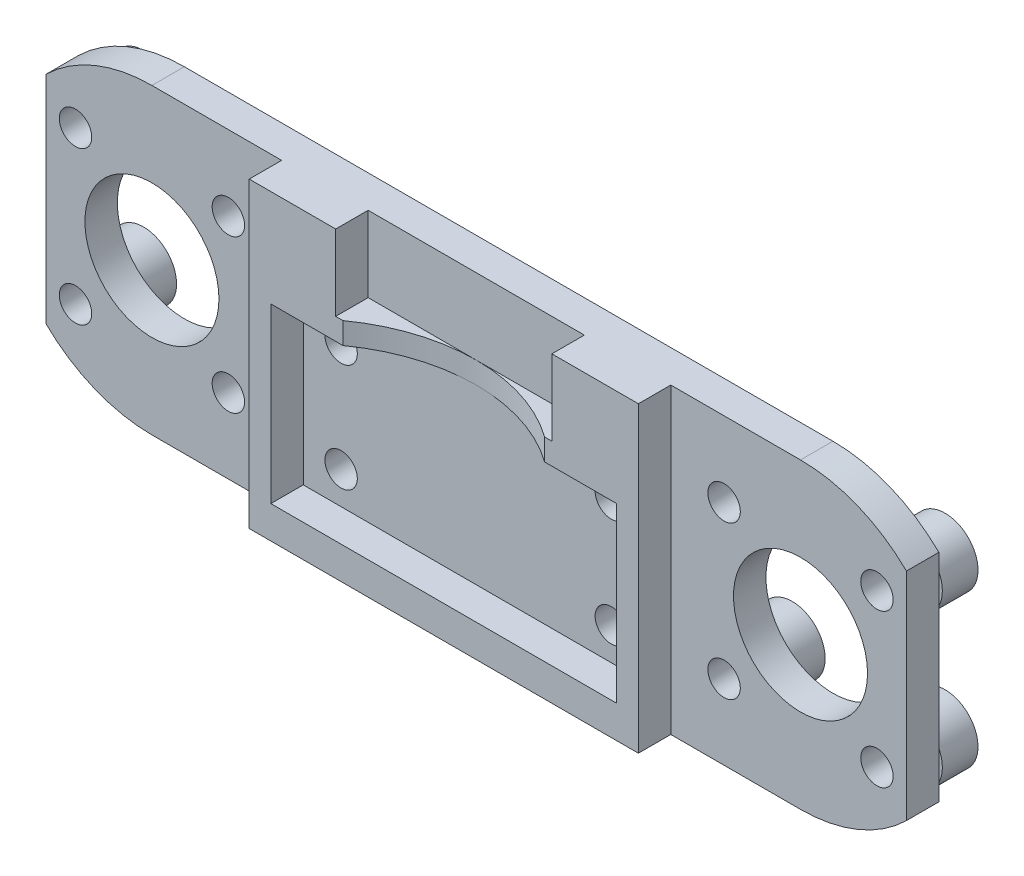
SolidWorks part; units mm, degrees
ref_plane "Front Plane" through (0, 0, 0) normal (0, 0, 1) x (1, 0, 0)
ref_plane "Top Plane" through (0, 0, 0) normal (0, 1, 0) x (1, 0, 0)
ref_plane "Right Plane" through (0, 0, 0) normal (1, 0, 0) x (0, 0, -1)
sketch "Sketch1" plane through (0, 0, 0) normal (0, 0, 1) x (1, 0, 0)
  line L0 (-39.8, 9.998) -> (-39.8, -9.998)
  line L1 (-30, -14) -> (30, -14)
  line L2 (-30, 14) -> (30, 14)
  line L6 (-30, 0) -> (30, 0) construction
  line L7 (39.8, 9.998) -> (39.8, -9.998)
  arc A0 (-30, 14) -> (-39.8, 9.998) centre (-30, 0) ccw
  arc A1 (-39.8, -9.998) -> (-30, -14) centre (-30, 0) ccw
  circle A2 centre (-30, 0) radius 6.2
  arc A7 (30, -14) -> (39.8, -9.998) centre (30, 0) ccw
  arc A8 (39.8, 9.998) -> (30, 14) centre (30, 0) ccw
  circle A9 centre (30, 0) radius 6.2
  point P7 (0, 0)
  point P8 (0, 0)
  point P18 (-30, 0)
  point P25 (30, 0)
  point P36 (30, 0)
  dimension "D2" = 9.8
  dimension "D3" = 12.4
  dimension "D4" = 14
  dimension "D1" = 28
  dimension "D7" = 60
extrude "Main" add sketch "Sketch1" along normal mid plane 3
sketch "Sketch2" plane through (0, 0, 1.5) normal (0, 0, -1) x (-1, 0, 0)
  line L0 (30, -14) -> (-30, -14) construction
  line L1 (39.8, 9.998) -> (39.8, -9.998) construction
  line L2 (18, 14) -> (10, 14)
  line L3 (18, 14) -> (18, -14)
  line L4 (18, -14) -> (-18, -14)
  line L5 (-18, 14) -> (-18, -14)
  line L6 (16, 5) -> (-16, 5)
  line L7 (16, 5) -> (16, -11)
  line L8 (16, -11) -> (-16, -11)
  line L9 (-16, 5) -> (-16, -11)
  line L10 (-39.8, -9.998) -> (-39.8, 9.998) construction
  line L11 (-30, 14) -> (30, 14) construction
  line L13 (-30, 14) -> (30, 14) construction
  line L14 (10, 14) -> (10, 7)
  line L15 (10, 7) -> (-10, 7)
  line L16 (-10, 7) -> (-10, 14)
  line L17 (-10, 14) -> (-18, 14)
  point P13 (0, -14)
  point P14 (0, 7)
  point P22 (0, 5)
  point P27 (16, -3)
  point P29 (0, -11)
  dimension "D1" = 16
  dimension "D2" = 36
  dimension "D4" = 7
  dimension "D5" = 32
  dimension "D6" = 79.6
  dimension "D9" = 3
  dimension "D10" = 2
  dimension "D11" = 20
  dimension "D12" = 3
extrude "Framework" add sketch "Sketch2" against normal blind 3
sketch "Sketch3" plane through (0, 0, -1.5) normal (0, 0, -1) x (-1, 0, 0)
  line L6 (16, 5) -> (16, -11) construction
  line L9 (16, -11) -> (-16, -11) construction
  circle A1 centre (12.5, -8) radius 1.5
  point P0 (16, -3)
  dimension "D1" = 3
  dimension "D2" = 5
  dimension "D3" = 12.5
  dimension "D4" = 8
  dimension "D5" = 3.5
  dimension "D6" = 3
extrude "FixHole" cut sketch "Sketch3" against normal through all
pattern_linear "HolePattern" count 2 spacing 25 along (1, 0, 0) count 2 spacing 10 along (0, 1, 0) of "FixHole"
sketch "Sketch4" plane through (0, 0, -1.5) normal (0, 0, 1) x (1, 0, 0)
  line L0 (-37.0711, 7.0711) -> (-22.9289, -7.0711) construction
  line L1 (-37.0711, -7.0711) -> (-22.9289, 7.0711) construction
  circle A0 centre (-37.0711, 7.0711) radius 3.05
  circle A1 centre (-22.9289, -7.0711) radius 3.05
  circle A2 centre (-22.9289, 7.0711) radius 3.05
  circle A3 centre (-37.0711, -7.0711) radius 3.05
  circle A4 centre (-37.0711, 7.0711) radius 1.5
  circle A5 centre (-22.9289, 7.0711) radius 1.5
  circle A6 centre (-30, 0) radius 6.2 construction
  circle A7 centre (-30, 0) radius 6.2 construction
  circle A8 centre (-37.0711, -7.0711) radius 1.5
  circle A9 centre (-22.9289, -7.0711) radius 1.5
  point P6 (-30, 0)
  point P10 (-30, 0)
  dimension "D1" = 6.1
  dimension "D3" = 3
  dimension "D2" = 20
extrude "ForLMK6UU" add sketch "Sketch4" against normal blind 3.3
sketch "Sketch5" plane through (0, 0, 1.5) normal (0, 0, 1) x (1, 0, 0)
  circle A0 centre (-37.0711, 7.0711) radius 1.5
  circle A1 centre (-37.0711, 7.0711) radius 1.5 construction
  circle A2 centre (-22.9289, 7.0711) radius 1.5
  circle A3 centre (-22.9289, 7.0711) radius 1.5 construction
  circle A4 centre (-37.0711, -7.0711) radius 1.5
  circle A5 centre (-37.0711, -7.0711) radius 1.5 construction
  circle A6 centre (-22.9289, -7.0711) radius 1.5
  circle A7 centre (-22.9289, -7.0711) radius 1.5 construction
extrude "Cut-Extrude1" cut sketch "Sketch5" against normal through all
mirror "Mirror1" about plane through (0, 0, 0) normal (1, 0, 0) of "Cut-Extrude1", "ForLMK6UU"
sketch "Sketch6" plane through (0, 7, 0) normal (0, 1, 0) x (1, 0, 0)
  line L0 (-10, -1.5) -> (10, -1.5) construction
  circle A0 centre (0, -17.5) radius 16
  point P2 (2.1465, -18.9291)
  dimension "D1" = 32
extrude "Cut-Extrude2" cut sketch "Sketch6" against normal up to surface (2 mm away) up to face at (0, 5, 3)
